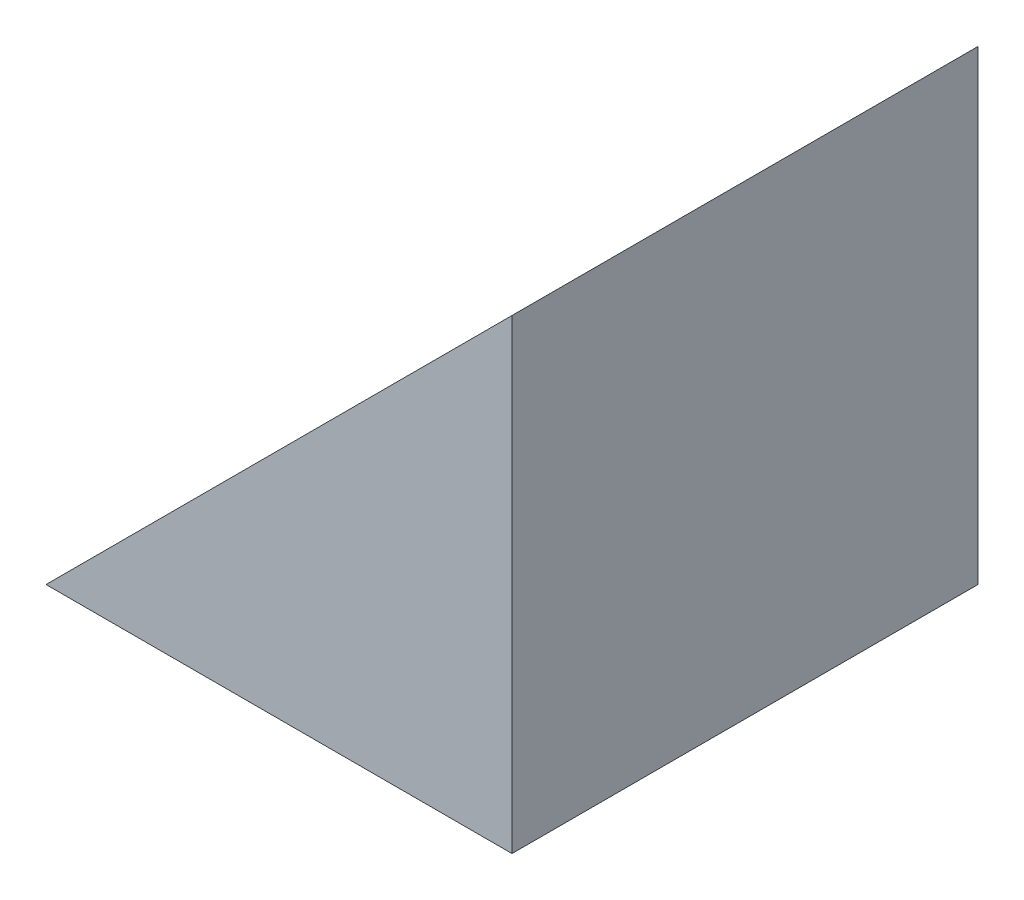
SolidWorks part; units mm, degrees
ref_plane "Front Plane" through (0, 0, 0) normal (0, 0, 1) x (1, 0, 0)
ref_plane "Top Plane" through (0, 0, 0) normal (0, 1, 0) x (1, 0, 0)
ref_plane "Right Plane" through (0, 0, 0) normal (1, 0, 0) x (0, 0, -1)
sketch "Sketch1" plane through (0, 0, 0) normal (0, 0, 1) x (1, 0, 0)
  line L0 (-14.5946, -17.5946) -> (15.4054, 12.4054)
  line L1 (-14.5946, -17.5946) -> (15.4054, -17.5946)
  line L4 (15.4054, -17.5946) -> (15.4054, 12.4054)
  dimension "D2" = 30
extrude "Boss-Extrude1" add sketch "Sketch1" along normal blind 30
